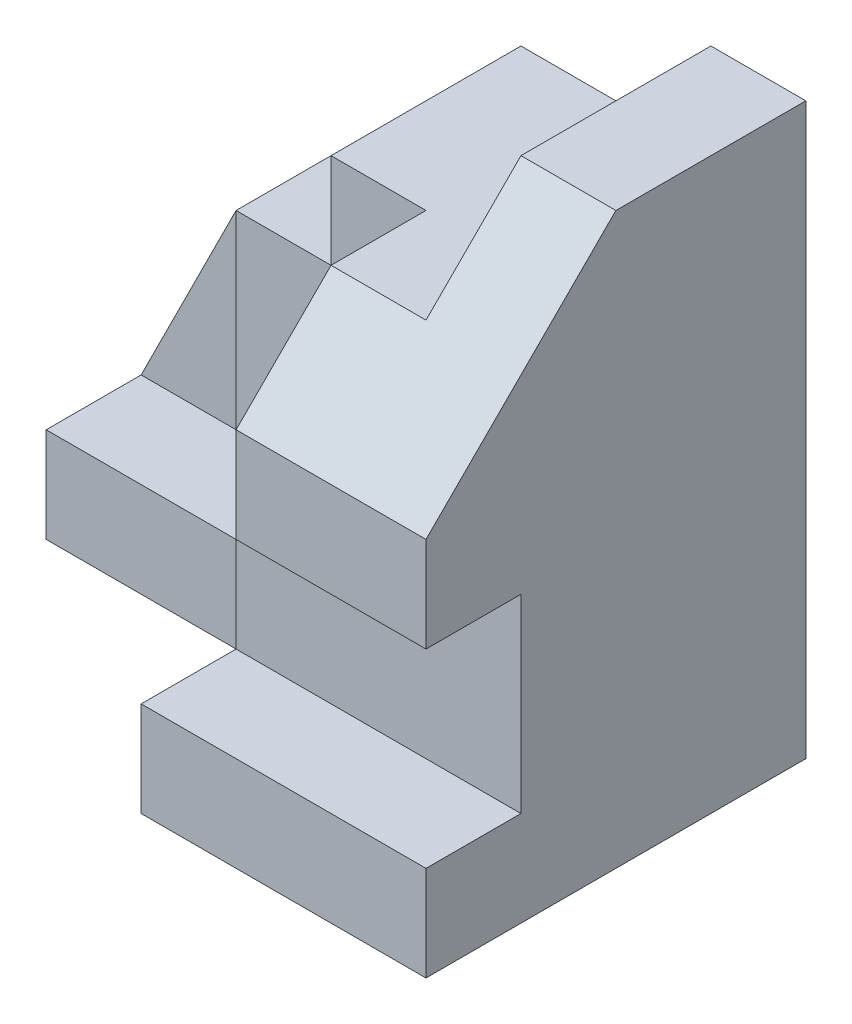
SolidWorks part; units mm, degrees
ref_plane "Front Plane" through (0, 0, 0) normal (0, 0, 1) x (1, 0, 0)
ref_plane "Top Plane" through (0, 0, 0) normal (0, 1, 0) x (1, 0, 0)
ref_plane "Right Plane" through (0, 0, 0) normal (1, 0, 0) x (0, 0, -1)
sketch "Sketch1" plane through (0, 0, 0) normal (0, 1, 0) x (1, 0, 0)
  line L0 (0, 0) -> (60, 0)
  line L1 (60, 0) -> (60, -40)
  line L2 (60, -40) -> (30, -40)
  line L3 (30, -40) -> (30, -20)
  line L4 (30, -20) -> (0, -20)
  line L5 (0, -20) -> (0, 0)
  dimension "D1" = 20
  dimension "D2" = 30
  dimension "D3" = 20
  dimension "D4" = 60
extrude "Boss-Extrude1" add sketch "Sketch1" along normal blind 60
sketch "Sketch2" plane through (0, 0, 40) normal (0, 0, 1) x (1, 0, 0)
  line L0 (50, 60) -> (50, 50)
  line L1 (30, 60) -> (60, 60) construction
  line L2 (50, 50) -> (30, 50)
  line L3 (0, 10) -> (10, 30)
  line L4 (0, 60) -> (0, 0) construction
  line L5 (10, 30) -> (20, 30)
  line L6 (30, 50) -> (30, 40)
  line L7 (30, 40) -> (20, 40)
  line L8 (20, 40) -> (20, 30)
  line L9 (0, 10) -> (0, 60)
  line L10 (0, 60) -> (50, 60)
  dimension "D1" = 10
  dimension "D2" = 20
  dimension "D3" = 10
  dimension "D4" = 10
  dimension "D5" = 10
  dimension "D6" = 10
  dimension "D7" = 50
  dimension "D8" = 20
extrude "Cut-Extrude1" cut sketch "Sketch2" against normal through all
sketch "Sketch3" plane through (0, 0, 20) normal (0, 0, 1) x (1, 0, 0)
  line L1 (20, 30) -> (0, 30)
  line L2 (20, 30) -> (20, 10)
  line L3 (20, 10) -> (0, 10)
  line L4 (0, 30) -> (0, 10)
extrude "Cut-Extrude2" cut sketch "Sketch3" against normal blind 10
chamfer "Chamfer1" distance 20 1 edges at (55, 60, 40)
sketch "Sketch4" plane through (0, 50, 0) normal (0, 1, 0) x (1, 0, 0)
  line L1 (30, -40) -> (40, -40)
  line L2 (30, -40) -> (30, -20)
  line L3 (30, -20) -> (40, -20)
  line L4 (40, -40) -> (40, -20)
  dimension "D1" = 20
  dimension "D2" = 10
extrude "Cut-Extrude3" cut sketch "Sketch4" against normal blind 30
sketch "Sketch5" plane through (30, 0, 0) normal (-1, 0, 0) x (0, 0, 1)
  line L0 (40, 20) -> (40, 0) construction
  line L1 (40, 10) -> (30, 10)
  line L2 (40, 10) -> (40, 30)
  line L3 (40, 30) -> (30, 30)
  line L4 (30, 10) -> (30, 30)
  line L5 (20, 0) -> (40, 0) construction
  dimension "D1" = 10
  dimension "D2" = 20
  dimension "D3" = 10
extrude "Cut-Extrude4" cut sketch "Sketch5" against normal blind 30
